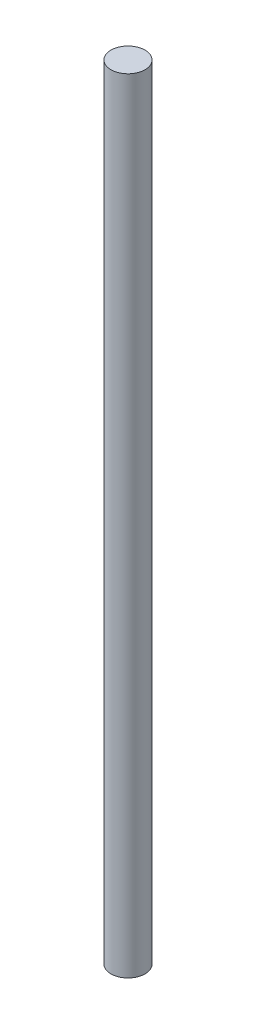
SolidWorks part; units mm, degrees
ref_plane "Front Plane" through (0, 0, 0) normal (0, 0, 1) x (1, 0, 0)
ref_plane "Top Plane" through (0, 0, 0) normal (0, 1, 0) x (1, 0, 0)
ref_plane "Right Plane" through (0, 0, 0) normal (1, 0, 0) x (0, 0, -1)
sketch "Sketch1" plane through (0, 0, 0) normal (0, 1, 0) x (1, 0, 0)
  circle A0 centre (0, 0) radius 5
  dimension "D1" = 10
extrude "Boss-Extrude1" add sketch "Sketch1" along normal blind 230
